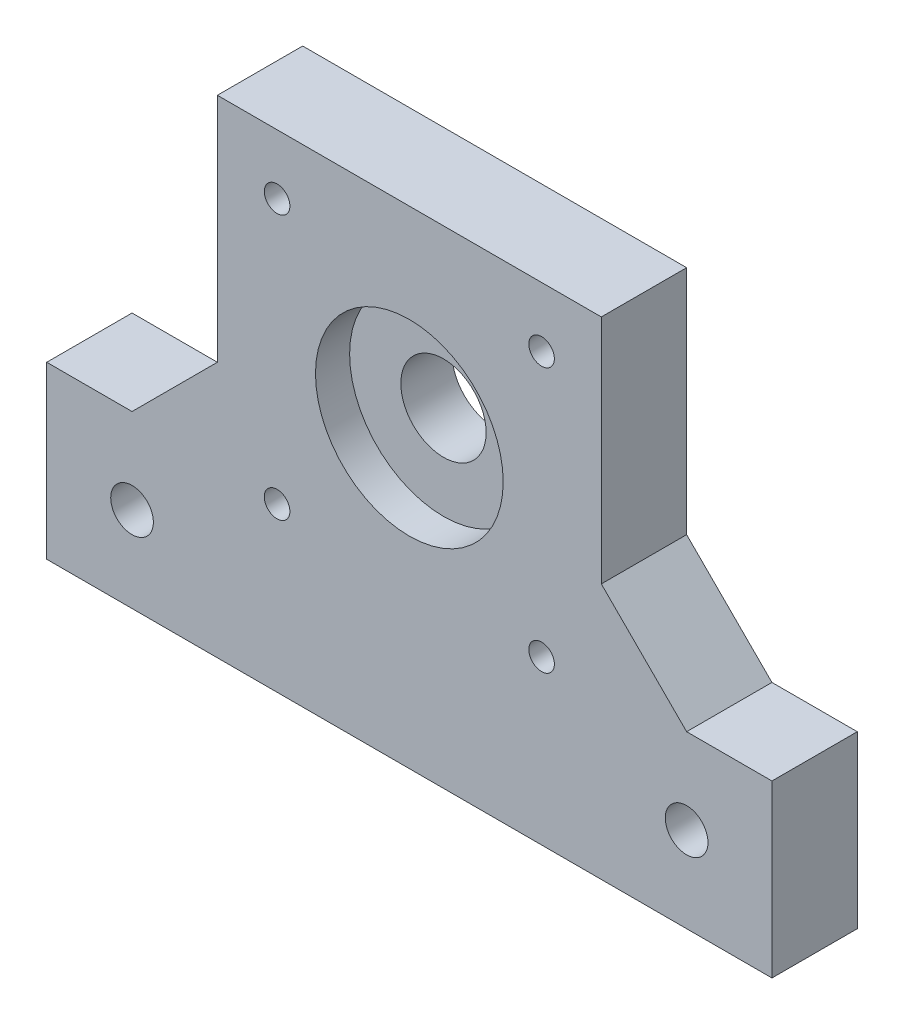
SolidWorks part; units mm, degrees
ref_plane "Front Plane" through (0, 0, 0) normal (0, 0, 1) x (1, 0, 0)
ref_plane "Top Plane" through (0, 0, 0) normal (0, 1, 0) x (1, 0, 0)
ref_plane "Right Plane" through (0, 0, 0) normal (1, 0, 0) x (0, 0, -1)
sketch "Sketch1" plane through (0, 0, 0) normal (0, 0, 1) x (1, 0, 0)
  line L0 (22.5, 22.5) -> (-22.5, 22.5)
  line L1 (-22.5, 22.5) -> (-22.5, -14.6)
  line L2 (-22.5, -14.6) -> (-42.5, -14.6)
  line L3 (-42.5, -14.6) -> (-42.5, -34.6)
  line L4 (-42.5, -34.6) -> (42.5, -34.6)
  line L5 (0, 22.5) -> (0, -34.6) construction
  line L6 (42.5, -14.6) -> (42.5, -34.6)
  line L7 (22.5, -14.6) -> (42.5, -14.6)
  line L8 (22.5, 22.5) -> (22.5, -14.6)
  line L9 (0, 0) -> (-22.5, 0) construction
  circle A1 centre (-15.5, 15.5) radius 1.5
  circle A2 centre (15.5, 15.5) radius 1.5
  circle A5 centre (32.5, -24.6) radius 2.5
  circle A6 centre (-32.5, -24.6) radius 2.5
  circle A7 centre (0, 0) radius 5
  circle A8 centre (15.5, -15.5) radius 1.5
  circle A9 centre (-15.5, -15.5) radius 1.5
  point P26 (42.5, -24.6)
  dimension "D4" = 10
  dimension "D5" = 3
  dimension "D9" = 5
  dimension "D11" = 31
  dimension "D1" = 20
  dimension "D2" = 45
  dimension "D3" = 20
  dimension "D6" = 31
  dimension "D7" = 14.6
  dimension "D8" = 7
  dimension "D10" = 65
extrude "Boss-Extrude1" add sketch "Sketch1" along normal blind 10
sketch "Sketch2" plane through (0, 0, 10) normal (0, 0, 1) x (1, 0, 0)
  circle A0 centre (0, 0) radius 11
  dimension "D1" = 22
extrude "Cut-Extrude1" cut sketch "Sketch2" against normal blind 4
chamfer "Chamfer1" distance 10 angle 45 2 edges at (-22.5, -14.6, 5) (22.5, -14.6, 5)
sketch "Sketch3" plane through (0, 0, 0) normal (0, 0, -1) x (-1, 0, 0)
  line L0 (0, 22.5) -> (0, 0) construction
  line L1 (-22.5, 22.5) -> (22.5, 22.5) construction
  line L2 (0, 0) -> (-22.5, 0) construction
  line L3 (-22.5, -4.6) -> (-22.5, 22.5) construction
  circle A0 centre (-15.5, 15.5) radius 2.85
  circle A1 centre (15.5, 15.5) radius 2.85
  circle A2 centre (-15.5, -15.5) radius 2.85
  circle A3 centre (15.5, -15.5) radius 2.85
  dimension "D1" = 5.7
extrude "Cut-Extrude2" cut sketch "Sketch3" against normal blind 4
